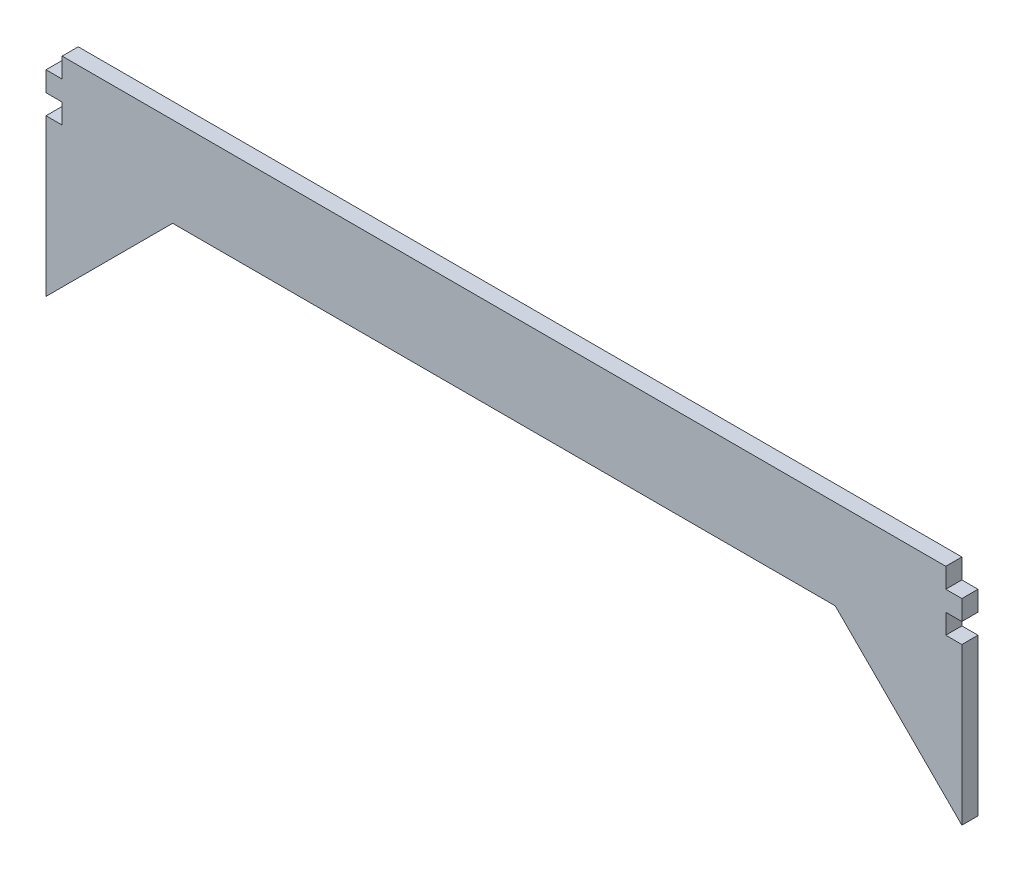
SolidWorks part; units mm, degrees
ref_plane "Ön Düzlem" through (0, 0, 0) normal (0, 0, 1) x (1, 0, 0)
ref_plane "Üst Düzlem" through (0, 0, 0) normal (0, 1, 0) x (1, 0, 0)
ref_plane "Sağ Düzlem" through (0, 0, 0) normal (1, 0, 0) x (0, 0, -1)
sketch "Sketch1" plane through (0, 0, 0) normal (0, 0, 1) x (1, 0, 0)
  line L0 (-76.7, -1.6667) -> (-76.7, 1.6667)
  line L3 (74, 5) -> (-74, 5)
  line L5 (76.7, 1.6667) -> (74, 1.6667)
  line L6 (-74, -1.6667) -> (-74, -5)
  line L8 (76.7, -1.6667) -> (76.7, 1.6667)
  line L10 (-76.7, 1.6667) -> (-74, 1.6667)
  line L11 (-74, 1.6667) -> (-74, 5)
  line L12 (-76.7, -1.6667) -> (-74, -1.6667)
  line L13 (74, 1.6667) -> (74, 5)
  line L14 (76.7, -1.6667) -> (74, -1.6667)
  line L15 (74, -1.6667) -> (74, -5)
  line L16 (-74, -5) -> (-76.7, -5)
  line L17 (-76.7, -5) -> (-76.7, -10)
  line L19 (76.7, -10) -> (76.7, -5)
  line L20 (76.7, -5) -> (74, -5)
  line L25 (-76.7, -31.2132) -> (-76.7, -10)
  line L26 (-55.4868, -10) -> (-76.7, -31.2132)
  line L30 (55.4868, -10) -> (76.7, -31.2132)
  line L31 (76.7, -31.2132) -> (76.7, -10)
  line L32 (-55.4868, -10) -> (55.4868, -10)
  point P0 (0, 0)
extrude "Boss-Extrude1" add sketch "Sketch1" along normal blind 2.7
